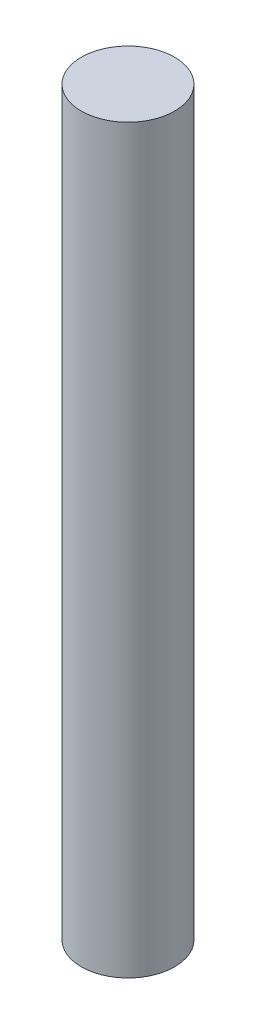
SolidWorks part; units mm, degrees
ref_plane "Front Plane" through (0, 0, 0) normal (0, 0, 1) x (1, 0, 0)
ref_plane "Top Plane" through (0, 0, 0) normal (0, 1, 0) x (1, 0, 0)
ref_plane "Right Plane" through (0, 0, 0) normal (1, 0, 0) x (0, 0, -1)
sketch "Sketch2" plane through (0, 0, 0) normal (0, 1, 0) x (1, 0, 0)
  circle A0 centre (0, 0) radius 6.3
extrude "Boss-Extrude1" add sketch "Sketch2" along normal blind 100
